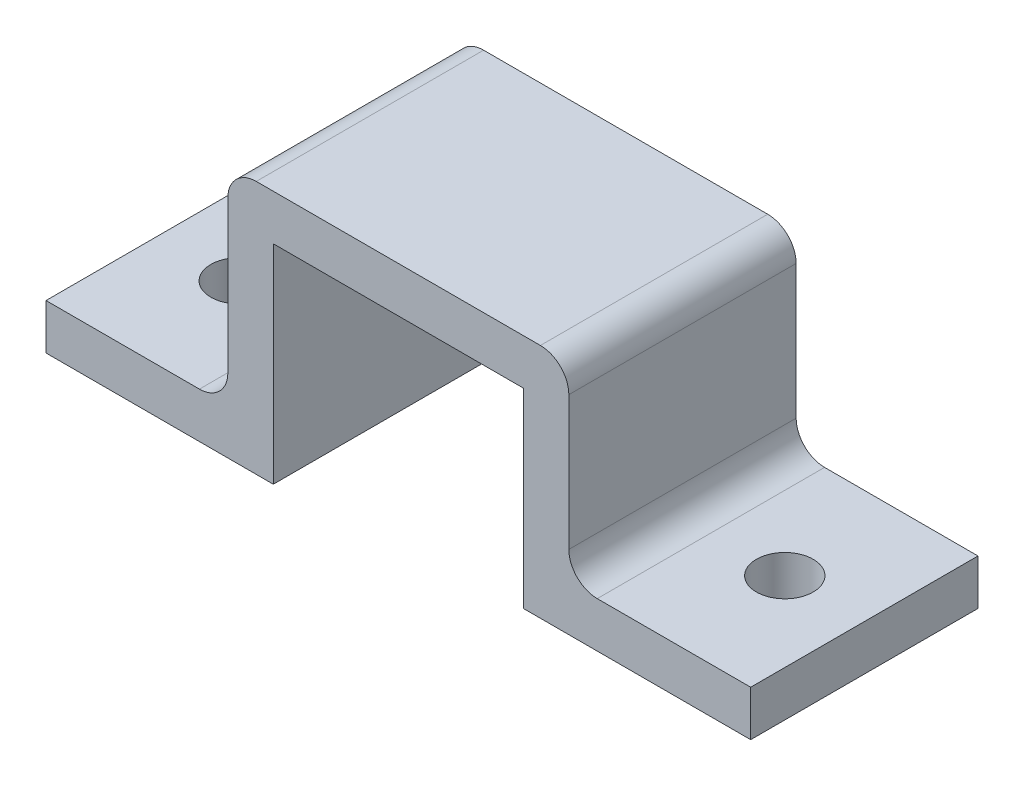
SolidWorks part; units mm, degrees
ref_plane "Front Plane" through (0, 0, 0) normal (0, 0, 1) x (1, 0, 0)
ref_plane "Top Plane" through (0, 0, 0) normal (0, 1, 0) x (1, 0, 0)
ref_plane "Right Plane" through (0, 0, 0) normal (1, 0, 0) x (0, 0, -1)
sketch "Sketch1" plane through (0, 0, 0) normal (0, 0, 1) x (1, 0, 0)
  line L0 (0, 0) -> (20, 0)
  line L1 (20, 0) -> (20, 18.3258)
  line L2 (20, 18.3258) -> (42, 18.3258)
  line L3 (42, 18.3258) -> (42, 1.5363)
  line L4 (62, 1.5363) -> (62, 5.5363)
  line L5 (62, 5.5363) -> (46, 5.5363)
  line L6 (46, 5.5363) -> (46, 22.3258)
  line L7 (16, 22.3258) -> (46, 22.3258)
  line L8 (16, 22.3258) -> (16, 4)
  line L9 (16, 4) -> (0, 4)
  line L10 (0, 4) -> (0, 0)
  line L11 (42, 1.5363) -> (62, 1.5363)
  dimension "D1" = 22
  dimension "D2" = 20
  dimension "D3" = 20
  dimension "D4" = 4
  dimension "D5" = 4
  dimension "D6" = 4
  dimension "D7" = 4
  dimension "D8" = 4
  dimension "D9" = 18.3258
  dimension "D10" = 20.7895
extrude "Boss-Extrude1" add sketch "Sketch1" along normal blind 20
fillet "Fillet2" radius 2.5 4 edges at (46, 5.5363, 10) (46, 22.3258, 10) (16, 22.3258, 10) (16, 4, 10)
sketch "Sketch2" plane through (0, 4, 0) normal (0, 1, 0) x (1, 0, 0)
  line L1 (0, -20) -> (0, 0) construction
  circle A0 centre (7, -10) radius 2.5
  point P4 (0, -10)
  dimension "D1" = 5
  dimension "D2" = 7
extrude "Cut-Extrude1" cut sketch "Sketch2" against normal blind 10
sketch "Sketch3" plane through (0, 5.5363, 0) normal (0, 1, 0) x (1, 0, 0)
  line L0 (62, -20) -> (62, 0) construction
  circle A0 centre (55, -10) radius 2.5
  point P4 (62, -10)
  dimension "D1" = 5
  dimension "D2" = 7
extrude "Cut-Extrude2" cut sketch "Sketch3" against normal blind 10
